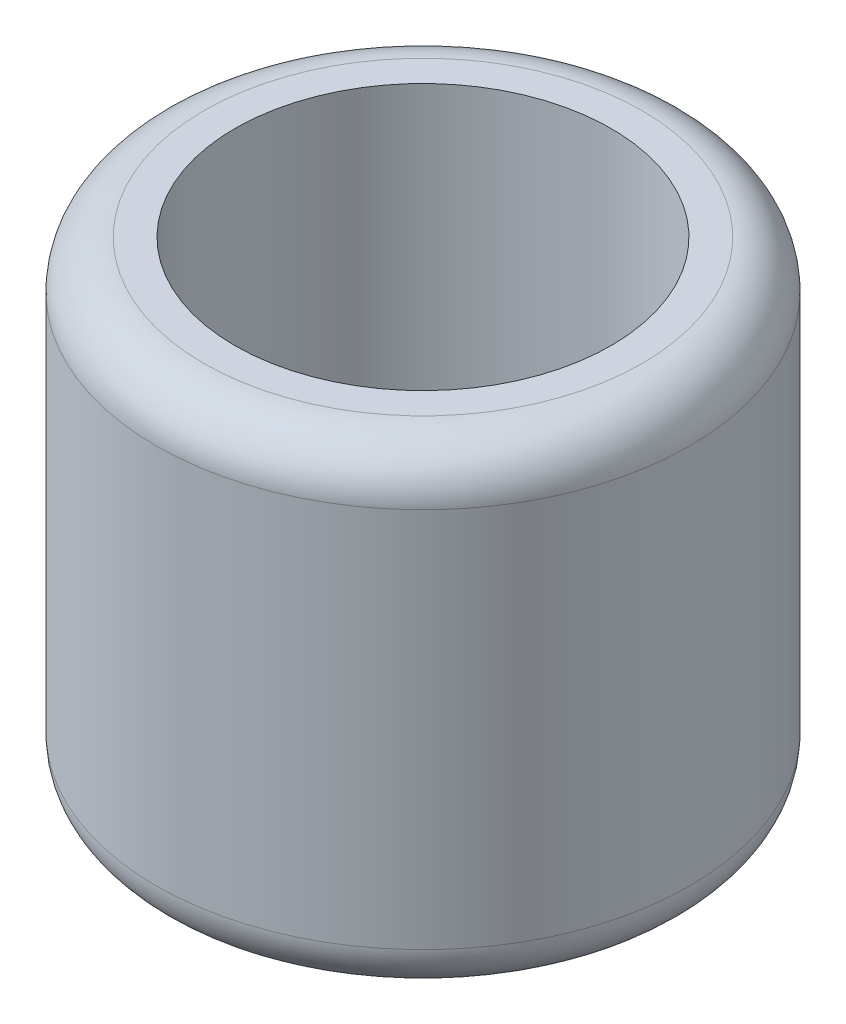
SolidWorks part; units mm, degrees
ref_plane "Front Plane" through (0, 0, 0) normal (0, 0, 1) x (1, 0, 0)
ref_plane "Top Plane" through (0, 0, 0) normal (0, 1, 0) x (1, 0, 0)
ref_plane "Right Plane" through (0, 0, 0) normal (1, 0, 0) x (0, 0, -1)
sketch "Sketch1" plane through (0, 0, 0) normal (0, 1, 0) x (1, 0, 0)
  circle A0 centre (0, 0) radius 3.95
  circle A1 centre (0, 0) radius 5.6
  dimension "D1" = 7.9
  dimension "D2" = 11.2
extrude "Boss-Extrude1" add sketch "Sketch1" along normal blind 10
fillet "Fillet1" radius 1 2 edges at (0, 0, 5.6) (0, 10, 5.6)
